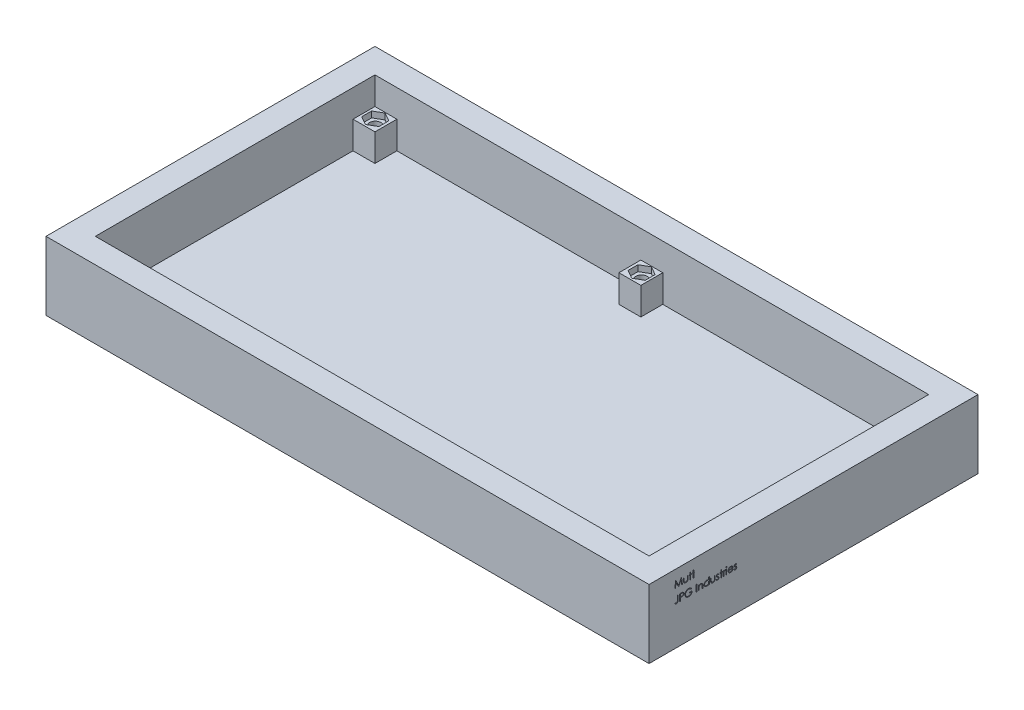
SolidWorks part; units mm, degrees
ref_plane "Front Plane" through (0, 0, 0) normal (0, 0, 1) x (1, 0, 0)
ref_plane "Top Plane" through (0, 0, 0) normal (0, 1, 0) x (1, 0, 0)
ref_plane "Right Plane" through (0, 0, 0) normal (1, 0, 0) x (0, 0, -1)
sketch "Sketch1" plane through (0, 0, 0) normal (0, 1, 0) x (1, 0, 0)
  line L1 (-131.0045, 48.4831) -> (125.5355, 48.4831)
  line L2 (-131.0045, 48.4831) -> (-131.0045, -81.0569)
  line L3 (-131.0045, -81.0569) -> (125.5355, -81.0569)
  line L4 (125.5355, 48.4831) -> (125.5355, -81.0569)
  dimension "D1" = 256.54
  dimension "D2" = 129.54
extrude "Extrude-Thin1" add sketch "Sketch1" along normal blind 25.4 thin thin type one direction wall 11.43
sketch "Sketch2" plane through (0, 0, 0) normal (0, -1, 0) x (1, 0, 0)
  line L1 (-142.4345, 92.4869) -> (136.9655, 92.4869)
  line L2 (-142.4345, 92.4869) -> (-142.4345, -59.9131)
  line L3 (-142.4345, -59.9131) -> (136.9655, -59.9131)
  line L4 (136.9655, 92.4869) -> (136.9655, -59.9131)
extrude "Boss-Extrude1" add sketch "Sketch2" along normal blind 6.35
sketch "Sketch6" plane through (0, 0, 0) normal (0, 1, 0) x (1, 0, 0)
  line L0 (-131.0045, -16.2869) -> (125.5355, -16.2869) construction
  line L1 (-131.0045, -81.0569) -> (-120.8445, -81.0569)
  line L2 (-131.0045, -81.0569) -> (-131.0045, -70.8969)
  line L3 (-131.0045, -70.8969) -> (-120.8445, -70.8969)
  line L4 (-120.8445, -81.0569) -> (-120.8445, -70.8969)
  line L5 (-131.0045, 48.4831) -> (-131.0045, -81.0569) construction
  line L6 (125.5355, -81.0569) -> (125.5355, 48.4831) construction
  line L7 (125.5355, -16.2869) -> (-2.7345, -81.0569) construction
  line L8 (-131.0045, -81.0569) -> (125.5355, -81.0569) construction
  line L9 (-2.7345, -81.0569) -> (-2.7345, 48.4831) construction
  line L10 (125.5355, 48.4831) -> (-131.0045, 48.4831) construction
  line L11 (-2.7345, 48.4831) -> (125.5355, -16.2869) construction
  line L12 (-131.0045, 48.4831) -> (-120.8445, 48.4831)
  line L13 (-131.0045, 48.4831) -> (-131.0045, 38.3231)
  line L14 (-131.0045, 38.3231) -> (-120.8445, 38.3231)
  line L15 (-120.8445, 48.4831) -> (-120.8445, 38.3231)
  line L16 (2.3455, -81.0569) -> (2.3455, -70.8969)
  line L17 (-7.8145, -81.0569) -> (2.3455, -81.0569)
  line L18 (-7.8145, -81.0569) -> (-7.8145, -70.8969)
  line L19 (-7.8145, -70.8969) -> (2.3455, -70.8969)
  line L20 (2.3455, 48.4831) -> (2.3455, 38.3231)
  line L21 (-7.8145, 38.3231) -> (2.3455, 38.3231)
  line L22 (-7.8145, 48.4831) -> (-7.8145, 38.3231)
  line L23 (-7.8145, 48.4831) -> (2.3455, 48.4831)
  line L24 (125.5355, -81.0569) -> (125.5355, -70.8969)
  line L25 (115.3755, -81.0569) -> (125.5355, -81.0569)
  line L26 (115.3755, -81.0569) -> (115.3755, -70.8969)
  line L27 (115.3755, -70.8969) -> (125.5355, -70.8969)
  line L28 (125.5355, 48.4831) -> (125.5355, 38.3231)
  line L29 (115.3755, 38.3231) -> (125.5355, 38.3231)
  line L30 (115.3755, 48.4831) -> (115.3755, 38.3231)
  line L31 (115.3755, 48.4831) -> (125.5355, 48.4831)
  dimension "D1" = 10.16
  dimension "D2" = 10.16
  dimension "D4" = 0
  dimension "D3" = 3
extrude "Boss-Extrude2" add sketch "Sketch6" along normal blind 12.7
sketch "Sketch7" plane through (136.9655, 0, 0) normal (1, 0, 0) x (0, 0, -1)
  text T0 "Mutt\r\nJPG Industries" font "Century Gothic" height 3.175
extrude "Cut-Extrude1" cut sketch "Sketch7" against normal blind 2.54
sketch "Sketch8" plane through (0, 12.7, 0) normal (0, 1, 0) x (1, 0, 0)
  line L0 (-131.0045, -70.8969) -> (-131.0045, -81.0569) construction
  line L1 (-126.0198, -71.6375) -> (-129.9885, -73.9288)
  line L2 (-129.9885, -73.9288) -> (-129.9885, -78.5115)
  line L3 (-129.9885, -78.5115) -> (-126.0198, -80.8029)
  line L4 (-126.0198, -80.8029) -> (-122.051, -78.5115)
  line L5 (-122.051, -78.5115) -> (-122.051, -73.9288)
  line L6 (-122.051, -73.9288) -> (-126.0198, -71.6375)
  line L7 (-131.0045, -81.0569) -> (-120.8445, -81.0569) construction
  line L8 (-120.8445, -81.0569) -> (-120.8445, -70.8969) construction
  circle A0 centre (-126.0198, -76.2202) radius 3.9688 construction
  dimension "D1" = 7.9375
  dimension "D2" = 1.016
  dimension "D3" = 0.254
  dimension "D4" = 10.16
  dimension "D5" = 1.2065
ref_plane "Plane1" through (0, 0, 16.2869) normal (0, 0, -1) x (-1, 0, 0)
ref_plane "Plane2" through (-2.7345, 0, 0) normal (1, 0, 0) x (0, 0, -1)
ref_plane "Plane3" through (-64.3295, 0, 0) normal (-1, 0, 0) x (0, 0, 1)
extrude "Cut-Extrude2" cut sketch "Sketch8" against normal blind 2.7781
hole_wizard "#6 (0.204) Diameter Hole2" positions "Sketch12" profile "Sketch13" hole size "#6" standard "ANSI Inch" end condition up to next
sketch "Sketch12" plane through (0, 9.9219, 0) normal (0, 1, 0) x (1, 0, 0)
  line L0 (-122.051, -78.5115) -> (-122.051, -73.9288) construction
  point P0 (-126.0198, -76.2202)
  point P12 (-122.051, -76.2202)
  dimension "D1" = 4.5827
  dimension "D2" = 3.9687
sketch "Sketch13" plane through (-126.0198, 9.9219, 76.2202) normal (1, 0, 0) x (0, 0, 1)
  line L0 (0, 0) -> (0, 16.2729)
  line L1 (0, 16.2729) -> (2.5908, 16.2729)
  line L2 (2.5908, 16.2729) -> (2.5908, 0)
  line L5 (2.5908, 0) -> (0, 0)
  line L11 (0, -6.35) -> (0, 107.95) construction
  dimension "Thru Hole Dia." = 5.1816
  dimension "Thru Hole Depth" = 16.2729
mirror "Mirror1" about plane through (0, 0, 16.2869) normal (0, 0, -1) of "#6 (0.204) Diameter Hole2", "Cut-Extrude2"
mirror "Mirror2" about plane through (-64.3295, 0, 0) normal (-1, 0, 0) of "#6 (0.204) Diameter Hole2", "Cut-Extrude2", "Mirror1"
mirror "Mirror4" about plane through (-2.7345, 0, 0) normal (1, 0, 0) of "#6 (0.204) Diameter Hole2", "Mirror1", "Cut-Extrude2"
sketch "Sketch14" plane through (136.9655, 0, 0) normal (1, 0, 0) x (0, 0, -1)
  line L0 (59.9131, 25.4) -> (59.9131, -6.35)
  line L1 (59.9131, -6.35) -> (98.0131, -6.35)
  spline S0 degree 2 poles (59.9131, 25.4) (76.1309, 6.1351) (98.0131, -6.35) knots 0 0 0 1 1 1
extrude "Axel Support" [suppressed] add sketch "Sketch14" against normal blind 57.15
mirror "Mirror18" [suppressed] about plane through (-2.7345, 0, 0) normal (1, 0, 0)
mirror "Mirror19" [suppressed] about plane through (0, 0, 16.2869) normal (0, 0, -1)
